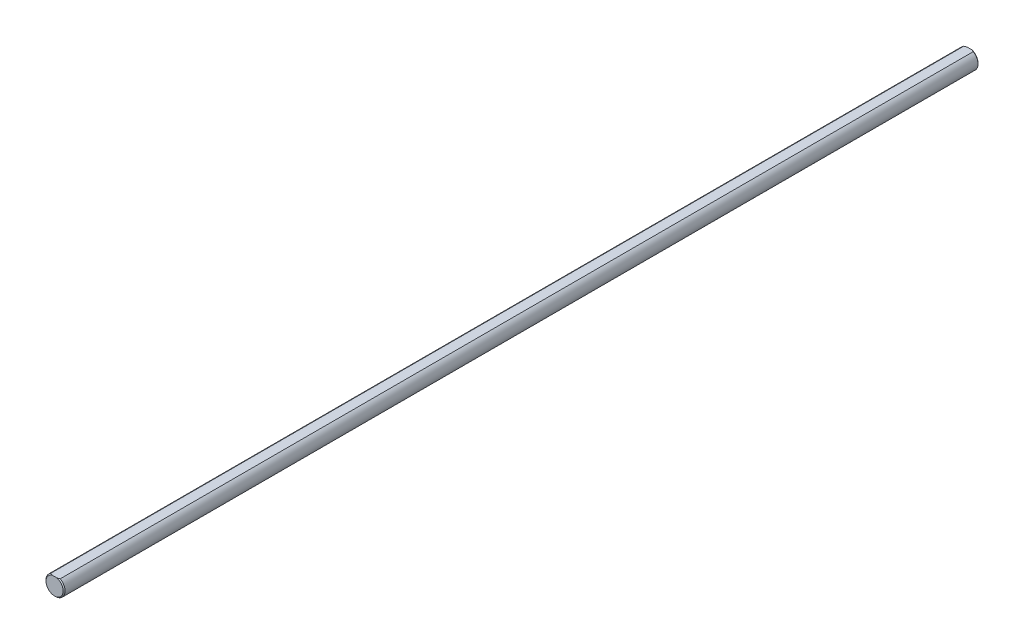
SolidWorks part; units mm, degrees
ref_plane "Front Plane" through (0, 0, 0) normal (0, 0, 1) x (1, 0, 0)
ref_plane "Top Plane" through (0, 0, 0) normal (0, 1, 0) x (1, 0, 0)
ref_plane "Right Plane" through (0, 0, 0) normal (1, 0, 0) x (0, 0, -1)
sketch "Sketch1" plane through (0, 0, 0) normal (0, 0, 1) x (1, 0, 0)
  circle A1 centre (0, 0) radius 3.175 construction
  dimension "Diameter" = 6.35
sketch "Sketch2" plane through (0, 0, 0) normal (1, 0, 0) x (0, 0, -1)
  line L0 (-152.4, 3.175) -> (152.4, 3.175) construction
  line L1 (0, 3.175) -> (0, -3.175) construction
  line L2 (0, 3.175) -> (0, -3.175) construction
  point P2 (0, 3.175)
  point P3 (139.7, 3.175)
  point P4 (-139.7, 3.175)
  dimension "Length" = 304.8
  dimension "D2" = 12.7
  dimension "D1" = 12.7
sketch "Sketch3" plane through (0, 0, 0) normal (0, 0, 1) x (1, 0, 0)
  circle A1 centre (0, 0) radius 3.175 construction
  circle A3 centre (0, 0) radius 3.175
extrude "Boss-Extrude2" add sketch "Sketch3" along normal up to vertex (152.4 mm away) and the other way up to vertex (152.4 mm away) up to point (0, 3.175, 152.4) other way up to point (0, 3.175, -152.4)
sketch "Sketch10" plane through (0, 0, 0) normal (0, 0, 1) x (1, 0, 0)
  line L0 (-1.5875, 2.7496) -> (1.5875, 2.7496)
  line L1 (0, 0) -> (0, 3.175) construction
  circle A0 centre (0, 0) radius 3.175 construction
  circle A1 centre (0, 0) radius 3.175 construction
  arc A2 (-1.5875, 2.7496) -> (1.5875, 2.7496) centre (0, 0) cw
extrude "Cut-Extrude5" cut sketch "Sketch10" against normal through all both and the other way through all
chamfer "Chamfer1" distance 0.3175 angle 45 4 edges at (0, -3.175, 152.4) (0, -3.175, -152.4) (0, 2.7496, -152.4) (0, 2.7496, 152.4)
equation "\"D1@Chamfer1\"= \"Diameter@Sketch1\" / 20"
equation "\"D1@Sketch2\"=\"Diameter@Sketch1\"*2"
equation "\"D2@Sketch2\"=\"D1@Sketch2\""
